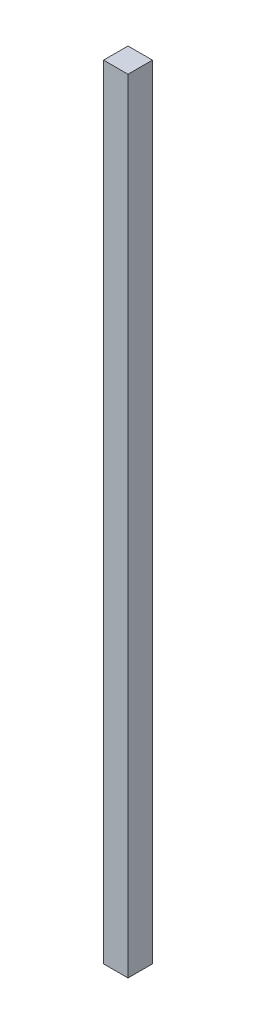
SolidWorks part; units mm, degrees
ref_plane "Front Plane" through (0, 0, 0) normal (0, 0, 1) x (1, 0, 0)
ref_plane "Top Plane" through (0, 0, 0) normal (0, 1, 0) x (1, 0, 0)
ref_plane "Right Plane" through (0, 0, 0) normal (1, 0, 0) x (0, 0, -1)
sketch "Sketch1" plane through (0, 0, 0) normal (0, 1, 0) x (1, 0, 0)
  line L1 (-19.05, 19.05) -> (19.05, 19.05)
  line L2 (-19.05, 19.05) -> (-19.05, -19.05)
  line L3 (-19.05, -19.05) -> (19.05, -19.05)
  line L4 (19.05, 19.05) -> (19.05, -19.05)
  line L5 (-19.05, 19.05) -> (19.05, -19.05) construction
  line L6 (-19.05, -19.05) -> (19.05, 19.05) construction
  point P0 (0, 0)
  dimension "D1" = 38.1
  dimension "D2" = 38.1
extrude "Boss-Extrude1" add sketch "Sketch1" along normal blind 1219.2
